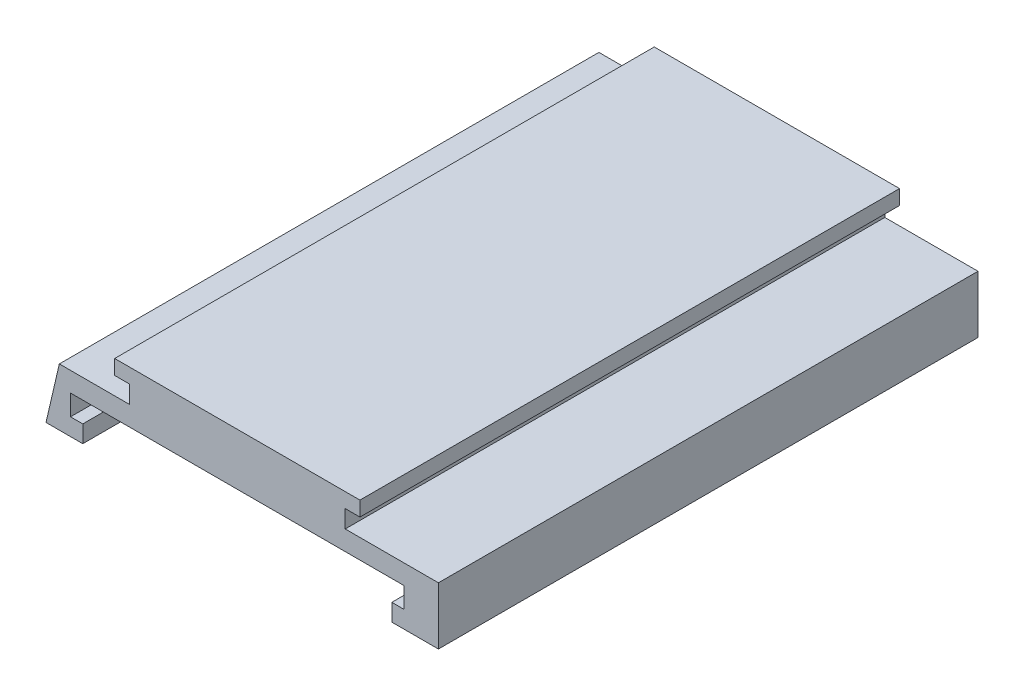
SolidWorks part; units mm, degrees
ref_plane "Front Plane" through (0, 0, 0) normal (0, 0, 1) x (1, 0, 0)
ref_plane "Top Plane" through (0, 0, 0) normal (0, 1, 0) x (1, 0, 0)
ref_plane "Right Plane" through (0, 0, 0) normal (1, 0, 0) x (0, 0, -1)
sketch "Sketch2" plane through (0, 0, 0) normal (0, 0, 1) x (1, 0, 0)
  line L0 (0, 0) -> (0, 5.85)
  line L1 (0, 0) -> (4.75, 0)
  line L2 (4.75, 0) -> (4.75, 1.75)
  line L3 (4.75, 1.75) -> (3.5, 1.75)
  line L4 (3.5, 1.75) -> (3.5, 3.85)
  line L5 (3.5, 3.85) -> (37.5, 3.85)
  line L6 (37.5, 3.85) -> (37.5, 1.75)
  line L7 (37.5, 1.75) -> (36.25, 1.75)
  line L8 (36.25, 1.75) -> (36.25, 0)
  line L9 (36.25, 0) -> (41, 0)
  line L10 (41, 0) -> (41, 5.85)
  line L11 (41, 5.85) -> (0, 5.85) construction
  line L12 (0, 5.85) -> (9.5, 5.85)
  line L13 (9.5, 5.85) -> (9.5, 7.65)
  line L14 (9.5, 7.65) -> (8, 7.65)
  line L15 (8, 7.65) -> (8, 9.15)
  line L16 (8, 9.15) -> (33, 9.15)
  line L17 (33, 9.15) -> (33, 7.65)
  line L18 (33, 7.65) -> (31.5, 7.65)
  line L19 (31.5, 7.65) -> (31.5, 5.85)
  line L20 (31.5, 5.85) -> (41, 5.85)
  point P11 (20.5, 5.85)
  point P14 (20.5, 3.85)
  point P15 (20.5, 9.15)
  dimension "D1" = 31.5
  dimension "D2" = 1.75
  dimension "D3" = 2.1
  dimension "D4" = 2
  dimension "D5" = 41
  dimension "D6" = 34
  dimension "D7" = 1.5
  dimension "D8" = 25
  dimension "D9" = 1.5
  dimension "D10" = 1.8
extrude "Boss-Extrude1" add sketch "Sketch2" along normal blind 55
sketch "Sketch3" plane through (0, 0, 55) normal (0, 0, 1) x (1, 0, 0)
  line L1 (0, 5.85) -> (0, 0) construction
  line L2 (0, 0) -> (4.75, 0) construction
  line L3 (1, 0) -> (0, 0)
  line L4 (0, 0) -> (0, 5.85)
  line L5 (1, 0) -> (2.3584, 5.85)
  line L6 (9.5, 5.85) -> (0, 5.85) construction
  line L7 (2.3584, 5.85) -> (0, 5.85)
  point P6 (2.9093, 5.85)
  point P9 (2.3584, 5.85)
  dimension "D2" = 1
extrude "Cut-Extrude2" cut sketch "Sketch3" against normal up to next
